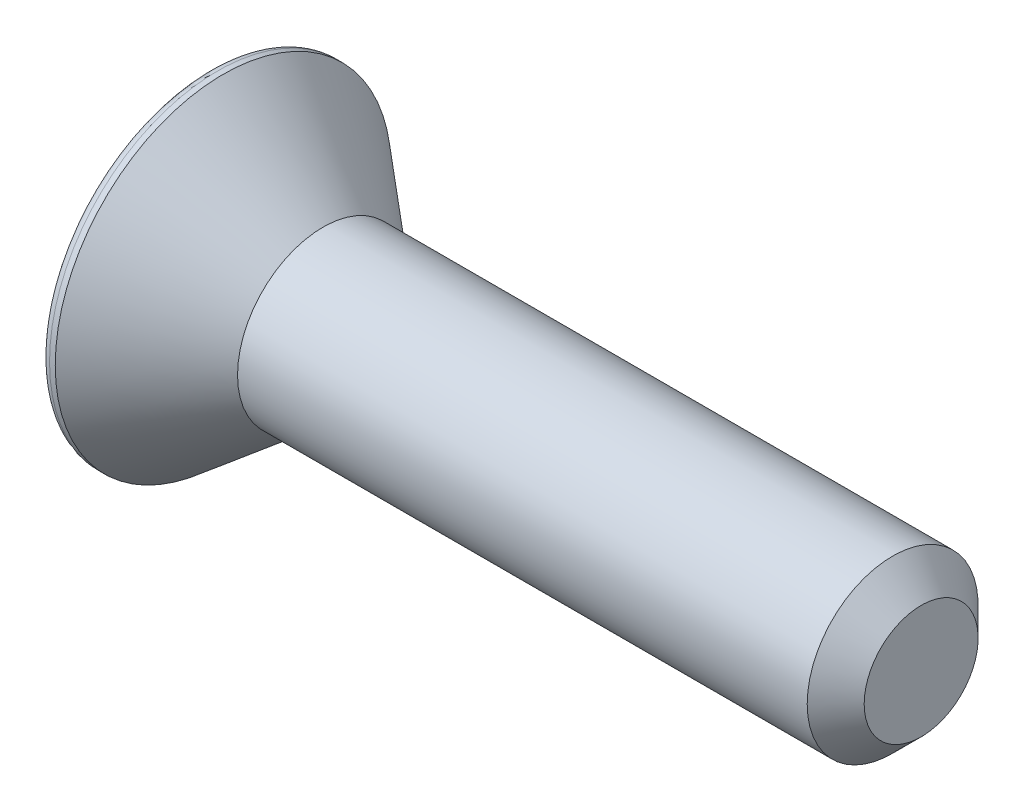
SolidWorks part; units mm, degrees
ref_plane "Спереди" through (0, 0, 0) normal (0, 0, 1) x (1, 0, 0)
ref_plane "Сверху" through (0, 0, 0) normal (0, 1, 0) x (1, 0, 0)
ref_plane "Справа" through (0, 0, 0) normal (1, 0, 0) x (0, 0, -1)
sketch "Эскиз1" plane through (0, 0, 0) normal (0, 0, 1) x (1, 0, 0)
  line L0 (0, 0) -> (0, 5.9)
  line L1 (0.5, 5.9) -> (4, 3)
  line L3 (4, 3) -> (25, 3)
  line L4 (25, 3) -> (25, 0)
  line L6 (0, 0) -> (25, 0)
  line L8 (0, 5.9) -> (0.5, 5.9)
  line L9 (0, 0) -> (-3.6011, 0) construction
  dimension "D4" = 0.5
  dimension "D1" = 4
  dimension "D2" = 11.8
  dimension "D3" = 6
  dimension "D5" = 25
revolve "Повернуть1" add sketch "Эскиз1" angle 360 about L6
cosmetic thread "Условное изображение резьбы1" parameters "D2"=4.891
sketch "Эскиз2" plane through (0, 0, 0) normal (-1, 0, 0) x (0, 0, 1)
  line L1 (1.1547, 2) -> (-1.1547, 2)
  line L2 (-1.1547, 2) -> (-2.3094, 0)
  line L3 (-2.3094, 0) -> (-1.1547, -2)
  line L4 (-1.1547, -2) -> (1.1547, -2)
  line L5 (1.1547, -2) -> (2.3094, 0)
  line L6 (2.3094, 0) -> (1.1547, 2)
  circle A0 centre (0, 0) radius 2 construction
  dimension "D1" = 4
extrude "Вырез-Вытянуть1" cut sketch "Эскиз2" against normal blind 3
fillet "Скругление1" radius 0.3 1 edges at (0, 0, 5.9)
chamfer "Фаска1" distance 1 angle 45 1 edges at (25, 0, 3)
